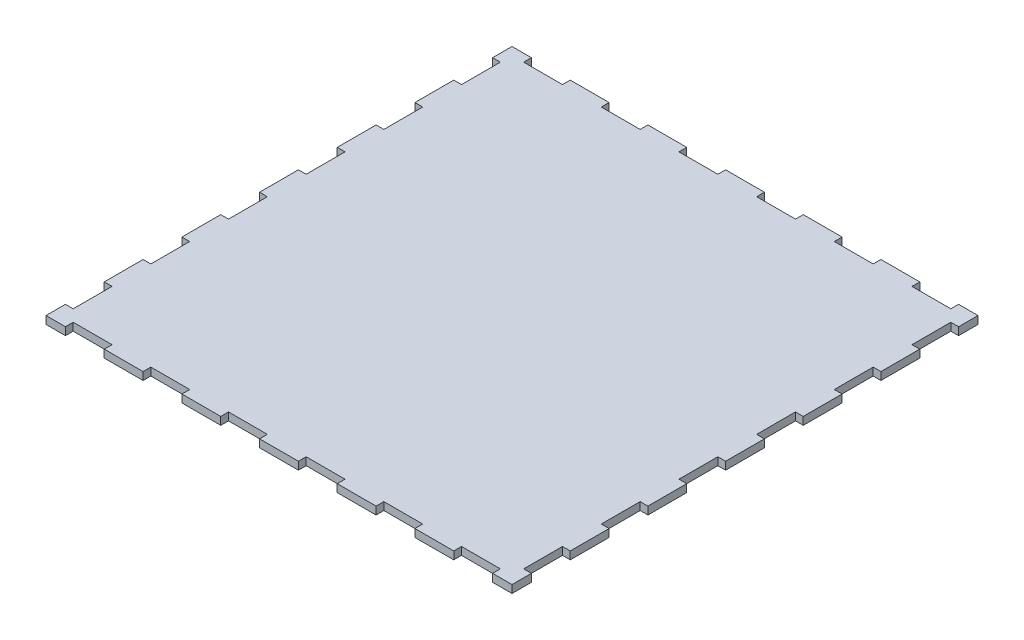
SolidWorks part; units mm, degrees
ref_plane "Front Plane" through (0, 0, 0) normal (0, 0, 1) x (1, 0, 0)
ref_plane "Top Plane" through (0, 0, 0) normal (0, 1, 0) x (1, 0, 0)
ref_plane "Right Plane" through (0, 0, 0) normal (1, 0, 0) x (0, 0, -1)
sketch "Sketch1" plane through (0, 0, 0) normal (0, 1, 0) x (1, 0, 0)
  line L0 (0, 152.4) -> (0, -152.4) construction
  line L1 (12.7, 152.4) -> (-12.7, 152.4)
  line L4 (-152.4, 152.4) -> (-152.4, 139.7)
  line L5 (0, 0) -> (152.4, 152.4) construction
  line L6 (0, 0) -> (-152.4, 152.4) construction
  line L7 (152.4, 0) -> (-152.4, 0) construction
  line L8 (-152.4, 12.7) -> (-147.32, 12.7)
  line L9 (-147.32, 12.7) -> (-147.32, 38.1)
  line L10 (-147.32, 38.1) -> (-152.4, 38.1)
  line L11 (-139.7, 152.4) -> (-152.4, 152.4)
  line L12 (-152.4, 88.9) -> (-147.32, 88.9)
  line L14 (-152.4, 63.5) -> (-147.32, 63.5)
  line L15 (-147.32, 88.9) -> (-147.32, 63.5)
  line L16 (-152.4, 139.7) -> (-147.32, 139.7)
  line L18 (-152.4, 114.3) -> (-147.32, 114.3)
  line L19 (-147.32, 139.7) -> (-147.32, 114.3)
  line L21 (-12.7, 152.4) -> (-12.7, 147.32)
  line L22 (-12.7, 147.32) -> (-38.1, 147.32)
  line L23 (-38.1, 152.4) -> (-38.1, 147.32)
  line L25 (-63.5, 152.4) -> (-63.5, 147.32)
  line L26 (-63.5, 147.32) -> (-88.9, 147.32)
  line L27 (-88.9, 152.4) -> (-88.9, 147.32)
  line L29 (-114.3, 152.4) -> (-114.3, 147.32)
  line L30 (-114.3, 147.32) -> (-139.7, 147.32)
  line L31 (-139.7, 152.4) -> (-139.7, 147.32)
  line L32 (-88.9, 152.4) -> (-114.3, 152.4)
  line L33 (-38.1, 152.4) -> (-63.5, 152.4)
  line L34 (-152.4, 114.3) -> (-152.4, 88.9)
  line L35 (-152.4, 63.5) -> (-152.4, 38.1)
  line L36 (-152.4, 12.7) -> (-152.4, -12.7)
  line L37 (152.4, 12.7) -> (152.4, -12.7)
  line L38 (152.4, 63.5) -> (152.4, 38.1)
  line L39 (152.4, 114.3) -> (152.4, 88.9)
  line L40 (38.1, 152.4) -> (63.5, 152.4)
  line L41 (88.9, 152.4) -> (114.3, 152.4)
  line L42 (139.7, 152.4) -> (139.7, 147.32)
  line L43 (114.3, 147.32) -> (139.7, 147.32)
  line L44 (114.3, 152.4) -> (114.3, 147.32)
  line L45 (88.9, 152.4) -> (88.9, 147.32)
  line L46 (63.5, 147.32) -> (88.9, 147.32)
  line L47 (63.5, 152.4) -> (63.5, 147.32)
  line L48 (38.1, 152.4) -> (38.1, 147.32)
  line L49 (12.7, 147.32) -> (38.1, 147.32)
  line L50 (147.32, 139.7) -> (147.32, 114.3)
  line L51 (152.4, 114.3) -> (147.32, 114.3)
  line L52 (152.4, 139.7) -> (147.32, 139.7)
  line L53 (147.32, 88.9) -> (147.32, 63.5)
  line L54 (152.4, 63.5) -> (147.32, 63.5)
  line L55 (152.4, 88.9) -> (147.32, 88.9)
  line L56 (139.7, 152.4) -> (152.4, 152.4)
  line L57 (147.32, 38.1) -> (152.4, 38.1)
  line L58 (147.32, 12.7) -> (147.32, 38.1)
  line L59 (152.4, 12.7) -> (147.32, 12.7)
  line L60 (152.4, 152.4) -> (152.4, 139.7)
  line L61 (0, 0) -> (-152.4, -152.4) construction
  line L62 (0, 0) -> (152.4, -152.4) construction
  line L63 (152.4, -152.4) -> (152.4, -139.7)
  line L64 (152.4, -12.7) -> (147.32, -12.7)
  line L65 (147.32, -12.7) -> (147.32, -38.1)
  line L66 (147.32, -38.1) -> (152.4, -38.1)
  line L67 (139.7, -152.4) -> (152.4, -152.4)
  line L68 (152.4, -88.9) -> (147.32, -88.9)
  line L69 (152.4, -63.5) -> (147.32, -63.5)
  line L70 (147.32, -88.9) -> (147.32, -63.5)
  line L71 (152.4, -139.7) -> (147.32, -139.7)
  line L72 (152.4, -114.3) -> (147.32, -114.3)
  line L73 (147.32, -139.7) -> (147.32, -114.3)
  line L74 (12.7, -147.32) -> (38.1, -147.32)
  line L75 (38.1, -152.4) -> (38.1, -147.32)
  line L76 (63.5, -152.4) -> (63.5, -147.32)
  line L77 (63.5, -147.32) -> (88.9, -147.32)
  line L78 (88.9, -152.4) -> (88.9, -147.32)
  line L79 (114.3, -152.4) -> (114.3, -147.32)
  line L80 (114.3, -147.32) -> (139.7, -147.32)
  line L81 (139.7, -152.4) -> (139.7, -147.32)
  line L82 (88.9, -152.4) -> (114.3, -152.4)
  line L83 (38.1, -152.4) -> (63.5, -152.4)
  line L84 (152.4, -114.3) -> (152.4, -88.9)
  line L85 (152.4, -63.5) -> (152.4, -38.1)
  line L86 (-152.4, -63.5) -> (-152.4, -38.1)
  line L87 (-152.4, -114.3) -> (-152.4, -88.9)
  line L88 (-38.1, -152.4) -> (-63.5, -152.4)
  line L89 (-88.9, -152.4) -> (-114.3, -152.4)
  line L90 (-139.7, -152.4) -> (-139.7, -147.32)
  line L91 (-114.3, -147.32) -> (-139.7, -147.32)
  line L92 (-114.3, -152.4) -> (-114.3, -147.32)
  line L93 (-88.9, -152.4) -> (-88.9, -147.32)
  line L94 (-63.5, -147.32) -> (-88.9, -147.32)
  line L95 (-63.5, -152.4) -> (-63.5, -147.32)
  line L96 (-38.1, -152.4) -> (-38.1, -147.32)
  line L97 (-12.7, -147.32) -> (-38.1, -147.32)
  line L98 (-12.7, -152.4) -> (-12.7, -147.32)
  line L99 (-147.32, -139.7) -> (-147.32, -114.3)
  line L100 (-152.4, -114.3) -> (-147.32, -114.3)
  line L101 (-152.4, -139.7) -> (-147.32, -139.7)
  line L102 (-147.32, -88.9) -> (-147.32, -63.5)
  line L103 (-152.4, -63.5) -> (-147.32, -63.5)
  line L104 (-152.4, -88.9) -> (-147.32, -88.9)
  line L105 (-139.7, -152.4) -> (-152.4, -152.4)
  line L106 (-147.32, -38.1) -> (-152.4, -38.1)
  line L107 (-147.32, -12.7) -> (-147.32, -38.1)
  line L108 (-152.4, -12.7) -> (-147.32, -12.7)
  line L109 (-152.4, -152.4) -> (-152.4, -139.7)
  line L110 (12.7, -152.4) -> (-12.7, -152.4)
  line L111 (12.7, 152.4) -> (12.7, 147.32)
  line L112 (12.7, -152.4) -> (12.7, -147.32)
  point P0 (0, 0)
  point P33 (-88.9, 149.86)
  dimension "D1" = 152.4
  dimension "D2" = 25.4
  dimension "D3" = 5.08
  dimension "D4" = 12.7
  dimension "D5" = 25.4
  dimension "D6" = 25.4
  dimension "D7" = 12.7
  dimension "D8" = 25.4
  dimension "D9" = 25.4
  dimension "D10" = 152.4
extrude "Boss-Extrude1" add sketch "Sketch1" along normal mid plane 5.08
